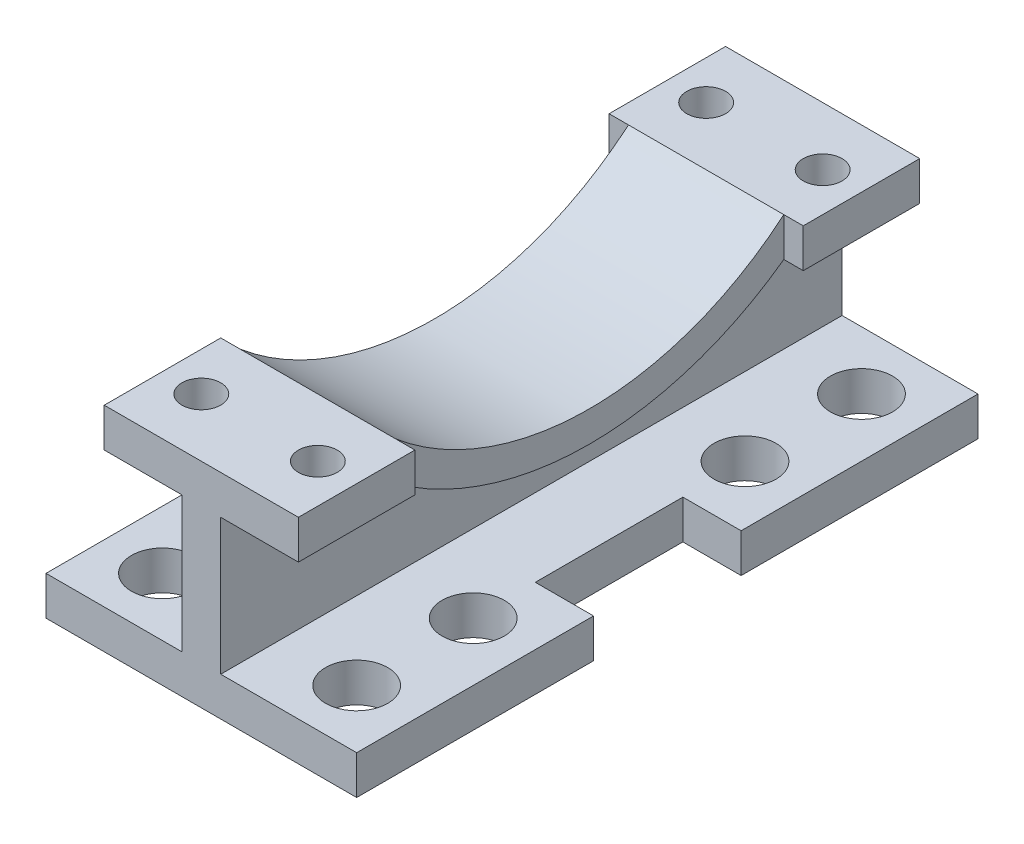
SolidWorks part; units mm, degrees
material "Plain Carbon Steel"
ref_plane "Front Plane" through (0, 0, 0) normal (0, 0, 1) x (1, 0, 0)
ref_plane "Top Plane" through (0, 0, 0) normal (0, 1, 0) x (1, 0, 0)
ref_plane "Right Plane" through (0, 0, 0) normal (1, 0, 0) x (0, 0, -1)
sketch "Sketch1" plane through (0, 0, 0) normal (0, 1, 0) x (1, 0, 0)
  line L0 (40, 160) -> (40, 0) construction
  line L1 (0, 160) -> (80, 160)
  line L2 (0, 160) -> (0, 0)
  line L3 (0, 0) -> (80, 0)
  line L4 (80, 160) -> (80, 0)
  line L5 (15, 0) -> (15, 160) construction
  line L6 (-15, 99) -> (15, 99)
  line L7 (-15, 99) -> (-15, 61)
  line L8 (-15, 61) -> (15, 61)
  line L9 (15, 99) -> (15, 61)
  line L10 (-15, 99) -> (15, 61) construction
  line L11 (-15, 61) -> (15, 99) construction
  line L12 (0, 145) -> (80, 145) construction
  line L13 (15, 145) -> (15, 115) construction
  line L14 (0, 80) -> (80, 80) construction
  line L15 (95, 61) -> (65, 61)
  line L16 (65, 99) -> (65, 61)
  line L17 (95, 99) -> (65, 99)
  line L18 (95, 99) -> (95, 61)
  circle A0 centre (15, 145) radius 8
  circle A1 centre (65, 145) radius 8
  circle A2 centre (15, 115) radius 8
  circle A3 centre (65, 115) radius 8
  circle A4 centre (15, 45) radius 8
  circle A5 centre (65, 45) radius 8
  circle A6 centre (65, 15) radius 8
  circle A7 centre (15, 15) radius 8
  point P4 (0, 80)
  dimension "D6" = 16
  dimension "D7" = 2
  dimension "D1" = 160
  dimension "D2" = 80
  dimension "D3" = 38
  dimension "D4" = 15
  dimension "D5" = 15
  dimension "D8" = 30
extrude "Boss-Extrude1" add sketch "Sketch1" along normal blind 10 contours L17 L4 L1 L2 L6 L9 L8 L3 L15 L16 A4 A1 A0 A2 A3 A5 A6 A7
ref_plane "Plane1" through (40, 0, 0) normal (1, 0, 0) x (0, 0, -1)
sketch "Sketch2" plane through (40, 0, 0) normal (1, 0, 0) x (0, 0, -1)
  line L0 (0, 0) -> (61, 0) construction
  line L1 (61, 0) -> (61, 10) construction
  line L2 (61, 10) -> (0, 10) construction
  line L3 (0, 10) -> (0, 0) construction
  line L4 (61, 0) -> (99, 0) construction
  line L5 (99, 0) -> (99, 10) construction
  line L6 (99, 10) -> (61, 10) construction
  line L7 (61, 10) -> (61, 0) construction
  line L8 (99, 0) -> (160, 0) construction
  line L9 (160, 0) -> (160, 10) construction
  line L10 (160, 10) -> (99, 10) construction
  line L11 (99, 10) -> (99, 0) construction
  line L12 (0, 0) -> (61, 0)
  line L13 (61, 0) -> (61, 10)
  line L14 (61, 10) -> (0, 10)
  line L15 (0, 10) -> (0, 0)
  line L16 (61, 0) -> (99, 0)
  line L17 (99, 0) -> (99, 10)
  line L18 (99, 10) -> (61, 10)
  line L19 (61, 10) -> (61, 0)
  line L20 (99, 0) -> (160, 0)
  line L21 (160, 0) -> (160, 10)
  line L22 (160, 10) -> (99, 10)
  line L23 (99, 10) -> (99, 0)
  line L25 (0, 10) -> (160, 10)
  line L26 (0, 10) -> (0, 45)
  line L27 (0, 45) -> (160, 45)
  line L28 (160, 10) -> (160, 45)
  dimension "D1" = 35
extrude "Boss-Extrude2" add sketch "Sketch2" along normal mid plane 10 contours L22 L28 L27 L26 L14 L18
sketch "Sketch4" plane through (0, 0, 0) normal (0, 1, 0) x (1, 0, 0)
  line L0 (40, 30) -> (40, 0) construction
  line L1 (35, 0) -> (45, 0) construction
  line L2 (15, 0) -> (65, 0)
  line L3 (45, 160) -> (35, 160) construction
  line L4 (80, 160) -> (45, 160) construction
  line L5 (15, 0) -> (15, 30)
  line L6 (45, 0) -> (80, 0) construction
  line L7 (80, 0) -> (80, 61) construction
  line L8 (80, 61) -> (65, 61) construction
  line L9 (65, 61) -> (65, 99) construction
  line L10 (65, 99) -> (80, 99) construction
  line L11 (80, 99) -> (80, 160) construction
  line L12 (15, 30) -> (65, 30)
  line L13 (35, 160) -> (0, 160) construction
  line L14 (0, 160) -> (0, 99) construction
  line L15 (0, 99) -> (15, 99) construction
  line L16 (15, 99) -> (15, 61) construction
  line L17 (15, 61) -> (0, 61) construction
  line L18 (0, 61) -> (0, 0) construction
  line L19 (0, 0) -> (35, 0) construction
  line L21 (35, 0) -> (45, 0)
  line L23 (45, 160) -> (35, 160)
  line L24 (80, 160) -> (45, 160)
  line L26 (45, 0) -> (80, 0)
  line L27 (80, 0) -> (80, 61)
  line L28 (80, 61) -> (65, 61)
  line L29 (65, 61) -> (65, 99)
  line L30 (65, 99) -> (80, 99)
  line L31 (80, 99) -> (80, 160)
  line L33 (35, 160) -> (0, 160)
  line L34 (0, 160) -> (0, 99)
  line L35 (0, 99) -> (15, 99)
  line L36 (15, 99) -> (15, 61)
  line L37 (15, 61) -> (0, 61)
  line L38 (0, 61) -> (0, 0)
  line L39 (0, 0) -> (35, 0)
  line L40 (65, 0) -> (65, 30)
  line L41 (15, 80) -> (65, 80) construction
  line L42 (15, 15) -> (65, 15) construction
  line L43 (40, 160) -> (40, 30) construction
  line L44 (15, 160) -> (65, 160)
  line L45 (65, 160) -> (65, 130)
  line L46 (15, 160) -> (15, 130)
  line L47 (15, 130) -> (65, 130)
  circle A0 centre (65, 145) radius 8 construction
  circle A1 centre (65, 115) radius 8 construction
  circle A2 centre (65, 15) radius 8 construction
  circle A3 centre (65, 45) radius 8 construction
  circle A4 centre (15, 15) radius 8 construction
  circle A5 centre (15, 45) radius 8 construction
  circle A6 centre (15, 115) radius 8 construction
  circle A7 centre (15, 145) radius 8 construction
  circle A8 centre (65, 145) radius 8
  circle A9 centre (65, 115) radius 8
  circle A10 centre (65, 15) radius 8
  circle A11 centre (65, 45) radius 8
  circle A12 centre (15, 15) radius 8
  circle A13 centre (15, 45) radius 8
  circle A14 centre (15, 115) radius 8
  circle A15 centre (15, 145) radius 8
  circle A18 centre (25, 15) radius 5
  circle A19 centre (55, 15) radius 5
  circle A20 centre (55, 145) radius 5
  circle A21 centre (25, 145) radius 5
  dimension "D4" = 10
  dimension "D5" = 10
  dimension "D1" = 30
  dimension "D2" = 15
  dimension "D3" = 15
ref_plane "Plane2" through (0, 45, 0) normal (0, -1, 0) x (-1, 0, 0)
sketch "Sketch7" plane through (0, 45, 0) normal (0, -1, 0) x (-1, 0, 0)
  line L0 (-15, 30) -> (-65, 30) construction
  line L1 (-65, 0) -> (-65, 30) construction
  line L2 (-15, 0) -> (-65, 0) construction
  line L3 (-15, 0) -> (-15, 30) construction
  line L4 (-15, 130) -> (-65, 130) construction
  line L5 (-65, 160) -> (-65, 130) construction
  line L6 (-15, 160) -> (-65, 160) construction
  line L7 (-15, 160) -> (-15, 130) construction
  line L8 (-15, 30) -> (-65, 30)
  line L9 (-65, 0) -> (-65, 30)
  line L10 (-15, 0) -> (-65, 0)
  line L11 (-15, 0) -> (-15, 30)
  line L12 (-15, 130) -> (-65, 130)
  line L13 (-65, 160) -> (-65, 130)
  line L14 (-15, 160) -> (-65, 160)
  line L15 (-15, 160) -> (-15, 130)
  circle A0 centre (-25, 145) radius 5 construction
  circle A1 centre (-55, 145) radius 5 construction
  circle A2 centre (-55, 15) radius 5 construction
  circle A3 centre (-25, 15) radius 5 construction
  circle A4 centre (-25, 145) radius 5
  circle A5 centre (-55, 145) radius 5
  circle A6 centre (-55, 15) radius 5
  circle A7 centre (-25, 15) radius 5
  point P0 (-65, 145)
extrude "Boss-Extrude3" add sketch "Sketch7" against normal blind 10
sketch "Sketch12" plane through (40, 0, 0) normal (1, 0, 0) x (0, 0, -1)
  line L0 (99, 0) -> (160, 0) construction
  line L1 (160, 0) -> (160, 10) construction
  line L2 (160, 10) -> (99, 10) construction
  line L3 (99, 10) -> (99, 0) construction
  line L4 (61, 0) -> (99, 0) construction
  line L5 (99, 0) -> (99, 10) construction
  line L6 (99, 10) -> (61, 10) construction
  line L7 (61, 10) -> (61, 0) construction
  line L8 (0, 0) -> (61, 0) construction
  line L9 (61, 0) -> (61, 10) construction
  line L10 (61, 10) -> (0, 10) construction
  line L11 (0, 10) -> (0, 0) construction
  line L12 (0, 10) -> (160, 10) construction
  line L13 (160, 10) -> (160, 45) construction
  line L14 (160, 45) -> (130, 45) construction
  line L15 (130, 45) -> (30, 45) construction
  line L16 (30, 45) -> (0, 45) construction
  line L17 (0, 45) -> (0, 10) construction
  line L18 (130, 45) -> (160, 45) construction
  line L19 (160, 45) -> (160, 55) construction
  line L20 (160, 55) -> (130, 55) construction
  line L21 (130, 55) -> (130, 45) construction
  line L22 (0, 45) -> (30, 45) construction
  line L23 (30, 45) -> (30, 55) construction
  line L24 (30, 55) -> (0, 55) construction
  line L25 (0, 55) -> (0, 45) construction
  line L26 (99, 0) -> (160, 0)
  line L27 (160, 0) -> (160, 10)
  line L28 (160, 10) -> (99, 10)
  line L29 (99, 10) -> (99, 0)
  line L30 (61, 0) -> (99, 0)
  line L31 (99, 0) -> (99, 10)
  line L32 (99, 10) -> (61, 10)
  line L33 (61, 10) -> (61, 0)
  line L34 (0, 0) -> (61, 0)
  line L35 (61, 0) -> (61, 10)
  line L36 (61, 10) -> (0, 10)
  line L37 (0, 10) -> (0, 0)
  line L38 (0, 10) -> (160, 10)
  line L39 (160, 10) -> (160, 45)
  line L40 (160, 45) -> (130, 45)
  line L41 (130, 45) -> (30, 45)
  line L42 (30, 45) -> (0, 45)
  line L43 (0, 45) -> (0, 10)
  line L44 (130, 45) -> (160, 45)
  line L45 (160, 45) -> (160, 55)
  line L46 (160, 55) -> (130, 55)
  line L47 (130, 55) -> (130, 45)
  line L48 (0, 45) -> (30, 45)
  line L49 (30, 45) -> (30, 55)
  line L50 (30, 55) -> (0, 55)
  line L51 (0, 55) -> (0, 45)
  arc A0 (30, 55) -> (130, 55) centre (80, 114.2136) ccw
  arc A1 (30, 45) -> (130, 45) centre (80, 114.2136) ccw
  dimension "D1" = 77.5
extrude "Boss-Extrude5" add sketch "Sketch12" along normal mid plane 40 contours L41 A1 A0 | A0 L49 L41 | A0 L41 L47
sketch "Sketch10" plane through (45, 0, 0) normal (1, 0, 0) x (0, 0, -1)
  line L1 (114.8673, 45) -> (45.1327, 45)
  line L2 (114.8673, 45) -> (45.1327, 45)
  arc A1 (45.1327, 45) -> (114.8673, 45) centre (80, 114.2136) ccw
  arc A3 (45.1327, 45) -> (114.8673, 45) centre (80, 114.2136) ccw
  dimension "D1" = 0
extrude "Cut-Extrude1" cut sketch "Sketch10" against normal mid plane 40
